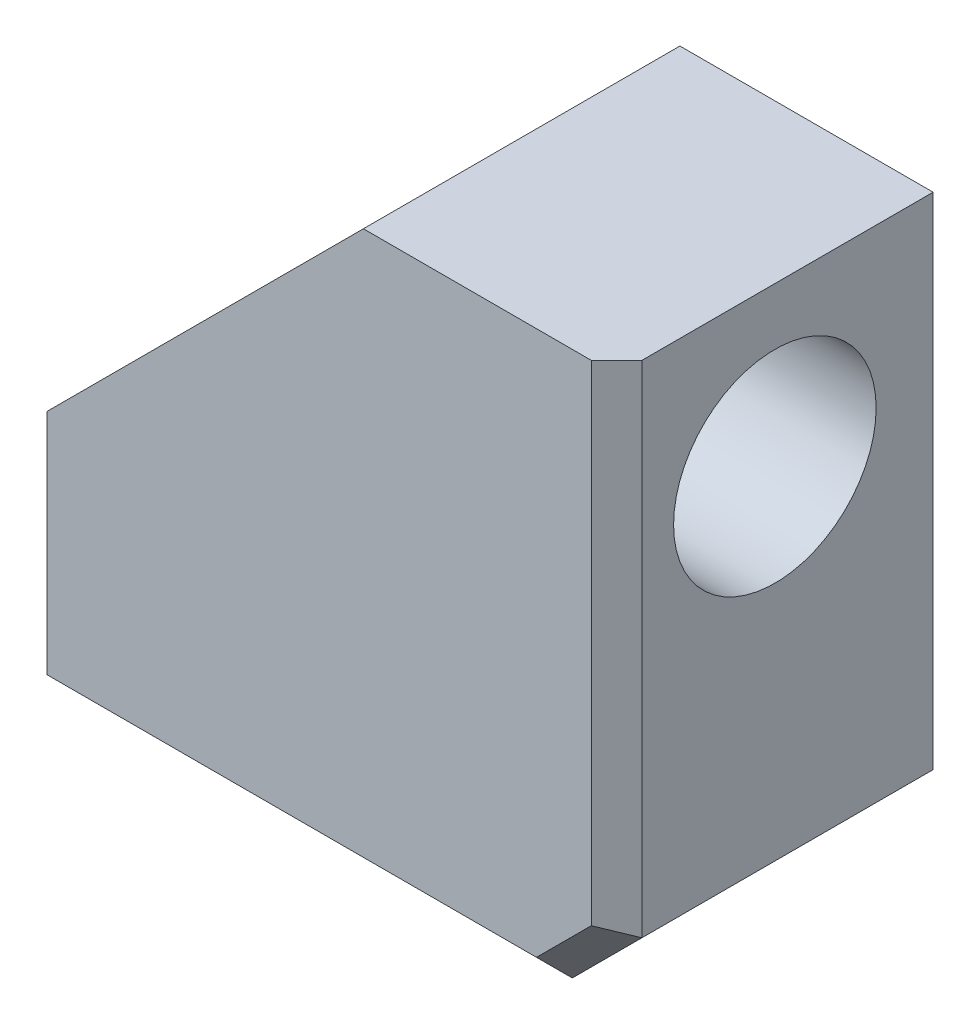
SolidWorks part; units mm, degrees
ref_plane "Front Plane" through (0, 0, 0) normal (0, 0, 1) x (1, 0, 0)
ref_plane "Top Plane" through (0, 0, 0) normal (0, 1, 0) x (1, 0, 0)
ref_plane "Right Plane" through (0, 0, 0) normal (1, 0, 0) x (0, 0, -1)
sketch "Sketch1" plane through (0, 0, 0) normal (0, 0, 1) x (1, 0, 0)
  line L0 (0, 4.5) -> (0, -4.5) construction
  line L1 (-4.5, 4.5) -> (4.5, 4.5)
  line L2 (-4.5, 4.5) -> (-4.5, -4.5)
  line L3 (-4.5, -4.5) -> (4.5, -4.5)
  line L4 (4.5, 4.5) -> (4.5, -4.5)
  dimension "D1" = 9
  dimension "D2" = 9
extrude "Boss-Extrude1" add sketch "Sketch1" along normal blind 5
sketch "Sketch2" plane through (0, 0, 0) normal (0, 0, -1) x (-1, 0, 0)
  line L0 (-4.5, -4.5) -> (-4.5, 4.5) construction
  line L1 (4.5, -4.5) -> (-4.5, -4.5) construction
  circle A0 centre (-2, -2) radius 1.6
  dimension "D1" = 3.2
  dimension "D2" = 2.5
  dimension "D3" = 2.5
extrude "Cut-Extrude1" cut sketch "Sketch2" against normal blind 4.5
sketch "Sketch3" plane through (4.5, 0, 0) normal (1, 0, 0) x (0, 0, -1)
  line L0 (-2.5, 4.5) -> (-2.5, -4.5) construction
  line L1 (-5, 4.5) -> (0, 4.5) construction
  line L2 (-5, -4.5) -> (0, -4.5) construction
  circle A0 centre (-2.5, 2) radius 1.6
  dimension "D1" = 3.2
  dimension "D2" = 2.5
extrude "Cut-Extrude2" cut sketch "Sketch3" against normal blind 4.5
sketch "Sketch4" plane through (0, -4.5, 0) normal (0, -1, 0) x (1, 0, 0)
  line L0 (-4.5, 2.5) -> (4.5, 2.5) construction
  line L1 (-4.5, 5) -> (-4.5, 0) construction
  line L2 (4.5, 5) -> (4.5, 0) construction
  circle A0 centre (-2, 2.5) radius 1.6
  dimension "D1" = 3.2
  dimension "D2" = 2.5
extrude "Cut-Extrude3" cut sketch "Sketch4" against normal blind 4.5
chamfer "Chamfer1" distance 1.1 angle 45 1 edges at (4.5, -4.5, 2.5)
chamfer "Chamfer2" distance 5 angle 45 1 edges at (-4.5, 4.5, 2.5)
chamfer "Chamfer3" distance 0.4 angle 45 3 edges at (4.5, 0.55, 5) (3.95, -3.95, 5) (-0.55, -4.5, 5)
